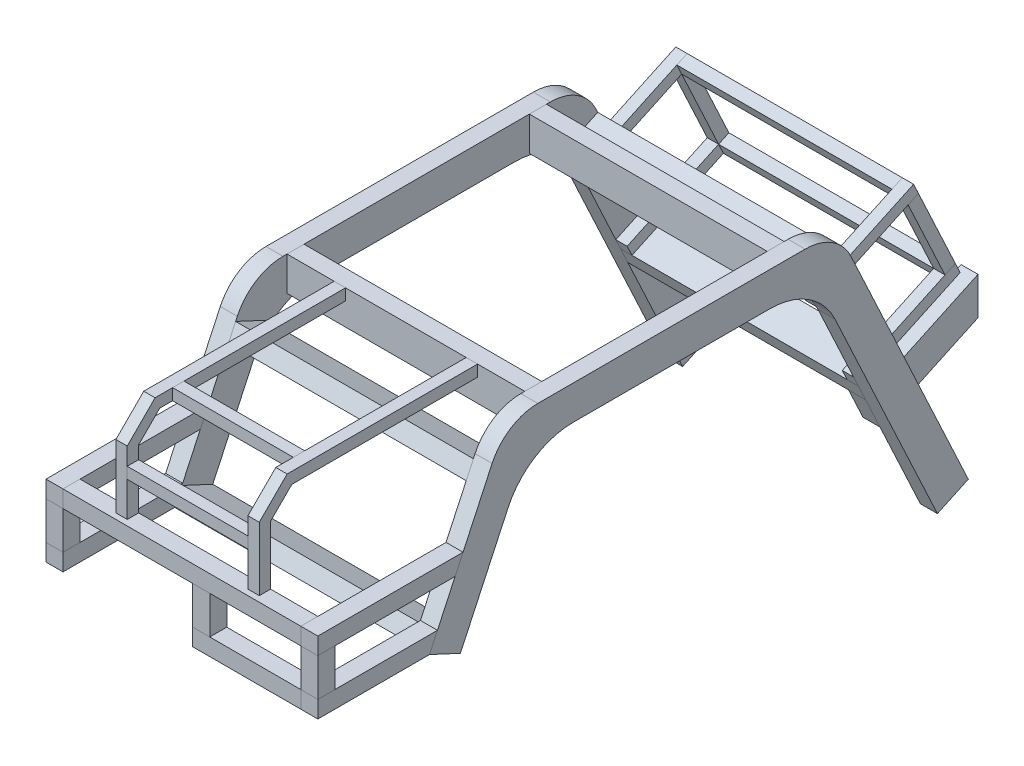
SolidWorks part; units mm, degrees
ref_plane "Front Plane" through (0, 0, 0) normal (0, 0, 1) x (1, 0, 0)
ref_plane "Top Plane" through (0, 0, 0) normal (0, 1, 0) x (1, 0, 0)
ref_plane "Right Plane" through (0, 0, 0) normal (1, 0, 0) x (0, 0, -1)
sketch "Sketch1" plane through (0, 0, 0) normal (1, 0, 0) x (0, 0, -1)
  line L1 (0, 30) -> (0, -30) construction
  line L33 (254, -30) -> (-254, -30)
  line L34 (292.2242, 30) -> (-292.2242, 30)
  line L35 (-372.0795, -283.2224) -> (-254, -30)
  line L36 (-426.458, -257.8653) -> (-292.2242, 30)
  line L39 (468.6901, -490.4044) -> (254, -30)
  line L40 (523.0685, -465.0473) -> (292.2242, 30)
  line L45 (523.0685, -465.0473) -> (468.6901, -490.4044)
  line L46 (-372.0795, -283.2224) -> (-426.458, -257.8653)
  point P2 (0, 0)
  dimension "D1" = 508
  dimension "D2" = 115
  dimension "D3" = 60
  dimension "D4" = 279.4
  dimension "D5" = 508
  dimension "D6" = 60
  dimension "D7" = 60
extrude "Boss-Extrude1" add sketch "Sketch1" against normal blind 30 from offset 239.55
sketch "Sketch2" plane through (239.55, 0, 0) normal (1, 0, 0) x (0, 0, -1)
  line L2 (-426.458, -257.8653) -> (-372.0795, -283.2224) construction
  line L6 (-381.3778, -161.1904) -> (-623.308, -161.1904)
  line L7 (-412.4688, -227.8654) -> (-623.308, -227.8654)
  line L10 (-367.3886, -131.1905) -> (-623.308, -131.1905)
  line L11 (-426.458, -257.8653) -> (-623.308, -257.8653)
  line L12 (-426.458, -257.8653) -> (-292.2242, 30) construction
  line L13 (-367.3886, -131.1905) -> (-381.3778, -161.1904)
  line L14 (-412.4688, -227.8654) -> (-426.458, -257.8653)
  line L15 (-623.308, -131.1905) -> (-623.308, -161.1904)
  line L16 (-623.308, -227.8654) -> (-623.308, -257.8653)
  dimension "D1" = 126.6748
  dimension "D2" = 255.9194
  dimension "D3" = 29.9999
extrude "Boss-Extrude2" add sketch "Sketch2" against normal up to surface (30 mm away) separate body up to face at (209.55, -187.0674, -24.1526)
sketch "Sketch12" plane through (239.55, 0, 0) normal (1, 0, 0) x (0, 0, -1)
  line L0 (-412.4688, -227.8654) -> (-623.308, -227.8654) construction
  line L1 (-623.308, -161.1904) -> (-593.3081, -161.1904)
  line L2 (-623.308, -161.1904) -> (-623.308, -227.8654)
  line L3 (-623.308, -227.8654) -> (-593.3081, -227.8654)
  line L4 (-593.3081, -161.1904) -> (-593.3081, -227.8654)
  line L5 (-623.308, -131.1905) -> (-623.308, -161.1904) construction
extrude "Boss-Extrude11" add sketch "Sketch12" against normal up to surface (30 mm away) separate body up to face at (209.55, -242.8654, 521.3857)
sketch "Sketch3" plane through (209.55, 0, 0) normal (-1, 0, 0) x (0, 0, 1)
  line L2 (228.6, 30) -> (228.6, -30)
  line L3 (264.7345, -53.0202) -> (319.113, -27.6631)
  line L4 (-254, -30) -> (254, -30) construction
  line L5 (292.2242, 30) -> (-292.2242, 30) construction
  line L6 (254, -30) -> (372.0795, -283.2224) construction
  line L7 (264.7345, -53.0202) -> (277.4131, -80.2095)
  line L8 (277.4131, -80.2095) -> (331.7915, -54.8524)
  line L9 (426.458, -257.8653) -> (292.2242, 30) construction
  line L10 (331.7915, -54.8524) -> (319.113, -27.6631)
  line L11 (228.6, 30) -> (198.6, 30)
  line L12 (198.6, 30) -> (198.6, -30)
  line L13 (198.6, -30) -> (228.6, -30)
  line L14 (372.0795, -283.2224) -> (426.458, -257.8653)
  line L15 (623.308, -131.1905) -> (593.3081, -131.1905)
  line L16 (623.308, -131.1905) -> (623.308, -161.1904)
  line L17 (623.308, -161.1904) -> (593.3081, -161.1904)
  line L18 (593.3081, -131.1905) -> (593.3081, -161.1904)
  line L19 (593.3081, -227.8654) -> (623.308, -227.8654)
  line L20 (593.3081, -227.8654) -> (593.3081, -257.8653)
  line L21 (593.3081, -257.8653) -> (623.308, -257.8653)
  line L22 (623.308, -227.8654) -> (623.308, -257.8653)
  line L23 (426.458, -257.8653) -> (413.7795, -230.6761)
  line L24 (413.7795, -230.6761) -> (359.401, -256.0332)
  line L25 (359.401, -256.0332) -> (372.0795, -283.2224)
  line L26 (0, 30) -> (0, -30) construction
  line L27 (-359.401, -256.0332) -> (-372.0795, -283.2224)
  line L28 (-413.7795, -230.6761) -> (-359.401, -256.0332)
  line L29 (-426.458, -257.8653) -> (-413.7795, -230.6761)
  line L30 (-372.0795, -283.2224) -> (-426.458, -257.8653)
  line L31 (-198.6, -30) -> (-228.6, -30)
  line L32 (-198.6, 30) -> (-198.6, -30)
  line L33 (-228.6, 30) -> (-198.6, 30)
  line L34 (-331.7915, -54.8524) -> (-319.113, -27.6631)
  line L35 (-277.4131, -80.2095) -> (-331.7915, -54.8524)
  line L36 (-264.7345, -53.0202) -> (-277.4131, -80.2095)
  line L37 (-264.7345, -53.0202) -> (-319.113, -27.6631)
  line L38 (-228.6, 30) -> (-228.6, -30)
  dimension "D1" = 30
  dimension "D2" = 25.4
  dimension "D3" = 25.4
extrude "Boss-Extrude3" add sketch "Sketch3" along normal blind 419.1 separate body
sketch "Sketch4" plane through (-209.55, 0, 0) normal (-1, 0, 0) x (0, 0, 1)
  line L8 (372.0795, -283.2224) -> (426.458, -257.8653)
  line L9 (254, -30) -> (372.0795, -283.2224)
  line L10 (-254, -30) -> (254, -30)
  line L11 (-468.6901, -490.4044) -> (-254, -30)
  line L12 (-523.0685, -465.0473) -> (-468.6901, -490.4044)
  line L13 (-292.2242, 30) -> (-523.0685, -465.0473)
  line L14 (292.2242, 30) -> (-292.2242, 30)
  line L15 (426.458, -257.8653) -> (292.2242, 30)
  line L16 (372.0795, -283.2224) -> (426.458, -257.8653)
  line L17 (254, -30) -> (372.0795, -283.2224)
  line L18 (-254, -30) -> (254, -30)
  line L19 (-468.6901, -490.4044) -> (-254, -30)
  line L20 (-523.0685, -465.0473) -> (-468.6901, -490.4044)
  line L21 (-292.2242, 30) -> (-523.0685, -465.0473)
  line L22 (292.2242, 30) -> (-292.2242, 30)
  line L23 (426.458, -257.8653) -> (292.2242, 30)
  dimension "D1" = 0
extrude "Boss-Extrude4" add sketch "Sketch4" along normal blind 30 separate body
sketch "Sketch5" plane through (-239.55, 0, 0) normal (-1, 0, 0) x (0, 0, 1)
  line L4 (623.308, -227.8654) -> (412.4688, -227.8654)
  line L6 (623.308, -257.8653) -> (623.308, -227.8654)
  line L7 (426.458, -257.8653) -> (623.308, -257.8653)
  line L8 (412.4688, -227.8654) -> (426.458, -257.8653)
  line L9 (623.308, -227.8654) -> (412.4688, -227.8654)
  line L10 (623.308, -257.8653) -> (623.308, -227.8654)
  line L11 (426.458, -257.8653) -> (623.308, -257.8653)
  line L12 (412.4688, -227.8654) -> (426.458, -257.8653)
  line L13 (381.3778, -161.1904) -> (623.308, -161.1904)
  line L14 (367.3886, -131.1905) -> (381.3778, -161.1904)
  line L15 (623.308, -131.1905) -> (367.3886, -131.1905)
  line L24 (623.308, -161.1904) -> (623.308, -131.1905)
  line L25 (381.3778, -161.1904) -> (623.308, -161.1904)
  line L26 (367.3886, -131.1905) -> (381.3778, -161.1904)
  line L27 (623.308, -131.1905) -> (367.3886, -131.1905)
  line L28 (623.308, -161.1904) -> (623.308, -131.1905)
  dimension "D1" = 0
  dimension "D2" = 0
extrude "Boss-Extrude5" add sketch "Sketch5" against normal up to surface (30 mm away) separate body up to face at (-209.55, -146.1905, 608.3081)
sketch "Sketch13" plane through (-239.55, 0, 0) normal (-1, 0, 0) x (0, 0, 1)
  line L4 (623.308, -161.1904) -> (593.3081, -161.1904)
  line L5 (593.3081, -161.1904) -> (593.3081, -227.8654)
  line L6 (593.3081, -227.8654) -> (623.308, -227.8654)
  line L7 (623.308, -227.8654) -> (623.308, -161.1904)
  line L8 (623.308, -161.1904) -> (593.3081, -161.1904)
  line L9 (593.3081, -161.1904) -> (593.3081, -227.8654)
  line L10 (593.3081, -227.8654) -> (623.308, -227.8654)
  line L11 (623.308, -227.8654) -> (623.308, -161.1904)
  dimension "D1" = 0
extrude "Boss-Extrude12" add sketch "Sketch13" against normal up to surface (30 mm away) separate body up to face at (-209.55, -146.1905, 498.8456)
sketch "Sketch6" plane through (-209.55, 0, 0) normal (-1, 0, 0) x (0, 0, 1)
  line L6 (-456.6807, 3.3844) -> (-277.4131, -80.2095)
  line L7 (-285.8654, -98.3356) -> (-465.1331, -14.7417)
  line L10 (-530.2163, -154.3131) -> (-350.9486, -237.907)
  line L11 (-538.6687, -172.4393) -> (-359.401, -256.0332)
  line L12 (-277.4131, -80.2095) -> (-285.8654, -98.3356)
  line L13 (-350.9486, -237.907) -> (-359.401, -256.0332)
  line L14 (-468.6901, -490.4044) -> (-254, -30) construction
  line L15 (-456.6807, 3.3844) -> (-465.1331, -14.7417)
  line L16 (-530.2163, -154.3131) -> (-538.6687, -172.4393)
  dimension "D1" = 20
  dimension "D2" = 197.8
extrude "Boss-Extrude6" add sketch "Sketch6" against normal blind 20 separate body
sketch "Sketch14" plane through (-209.55, 0, 0) normal (-1, 0, 0) x (0, 0, 1)
  line L0 (-465.1331, -14.7417) -> (-530.2163, -154.3131)
  line L1 (-530.2163, -154.3131) -> (-512.0902, -162.7655)
  line L2 (-350.9486, -237.907) -> (-530.2163, -154.3131) construction
  line L3 (-512.0902, -162.7655) -> (-447.0069, -23.1941)
  line L4 (-465.1331, -14.7417) -> (-285.8654, -98.3356) construction
  line L5 (-447.0069, -23.1941) -> (-465.1331, -14.7417)
  line L6 (-456.6807, 3.3844) -> (-465.1331, -14.7417) construction
extrude "Boss-Extrude13" add sketch "Sketch14" against normal up to surface (20 mm away) separate body up to face at (-189.55, -47.4756, -371.2731)
ref_plane "Mid" through (0, 0, 0) normal (-1, 0, 0) x (0, 0, 1)
ref_plane "Half" through (0, 0, 0) normal (0, 0, -1) x (-1, 0, 0)
mirror "Mirror1" about plane through (0, 0, 0) normal (-1, 0, 0) of bodies 131 130 132 114
sketch "Sketch7" plane through (189.55, 0, 0) normal (-1, 0, 0) x (0, 0, 1)
  line L0 (-447.0069, -23.1941) -> (-438.5546, -5.0679)
  line L1 (-277.4131, -80.2095) -> (-456.6807, 3.3844) construction
  line L2 (-438.5546, -5.0679) -> (-456.6807, 3.3844)
  line L3 (-456.6807, 3.3844) -> (-465.1331, -14.7417)
  line L4 (-512.0902, -162.7655) -> (-447.0069, -23.1941) construction
  line L5 (-465.1331, -14.7417) -> (-447.0069, -23.1941)
  line L6 (-512.0902, -162.7655) -> (-520.5425, -180.8916)
  line L7 (-538.6687, -172.4393) -> (-359.401, -256.0332) construction
  line L8 (-520.5425, -180.8916) -> (-538.6687, -172.4393)
  line L9 (-538.6687, -172.4393) -> (-530.2163, -154.3131)
  line L10 (-530.2163, -154.3131) -> (-512.0902, -162.7655)
  line L11 (-350.9486, -237.907) -> (-530.2163, -154.3131) construction
extrude "Boss-Extrude7" add sketch "Sketch7" along normal up to surface (379.1 mm away) separate body up to face at (-189.55, -205.1731, -444.8087)
ref_plane "Sensor Mount" through (-126.36, 0, 0) normal (1, 0, 0) x (0, 0, -1)
sketch "Sketch8" plane through (-126.36, 0, 0) normal (-1, 0, 0) x (0, 0, 1)
  line L2 (613.3081, -19.0833) -> (613.3081, -131.1905)
  line L3 (593.3081, -27.3676) -> (593.3081, -131.1905)
  line L6 (613.3081, -19.0833) -> (564.2248, 30)
  line L7 (555.9405, 10) -> (593.3081, -27.3676)
  line L10 (564.2248, 30) -> (228.6, 30)
  line L11 (555.9405, 10) -> (228.6, 10)
  line L12 (228.6, 30) -> (228.6, 10)
  line L13 (593.3081, -131.1905) -> (613.3081, -131.1905)
  dimension "D1" = 45
  dimension "D2" = 20
  dimension "D3" = 20
  dimension "D4" = 20
  dimension "D5" = 103.823
extrude "Boss-Extrude8" add sketch "Sketch8" against normal blind 20 separate body
mirror "Mirror2" about plane through (0, 0, 0) normal (-1, 0, 0) of bodies 118
sketch "Sketch9" plane through (-106.36, 0, 0) normal (1, 0, 0) x (0, 0, -1)
  line L2 (-533.3106, 30) -> (-533.3106, 10)
  line L3 (-613.3081, -49.9975) -> (-593.3081, -49.9975)
  line L4 (-613.3081, -131.1905) -> (-613.3081, -19.0833) construction
  line L6 (-228.6, 10) -> (-555.9405, 10) construction
  line L8 (-533.3106, 30) -> (-513.3106, 30)
  line L9 (-564.2248, 30) -> (-228.6, 30) construction
  line L10 (-513.3106, 30) -> (-513.3106, 10)
  line L11 (-513.3106, 10) -> (-533.3106, 10)
  line L12 (-593.3081, -49.9975) -> (-593.3081, -69.9975)
  line L13 (-593.3081, -27.3676) -> (-593.3081, -131.1905) construction
  line L14 (-593.3081, -69.9975) -> (-613.3081, -69.9975)
  line L15 (-613.3081, -69.9975) -> (-613.3081, -49.9975)
  dimension "D1" = 20
  dimension "D2" = 22.6299
  dimension "D3" = 22.6299
extrude "Boss-Extrude9" add sketch "Sketch9" along normal up to surface (212.72 mm away) separate body up to face at (106.36, -28.604, 498.8247)
sketch "Sketch10" plane through (0, 0, 623.308) normal (0, 0, 1) x (1, 0, 0)
  line L5 (209.55, -237.907) -> (209.55, -154.3131) construction
  line L7 (19.0501, -227.8654) -> (19.0501, -161.1904)
  line L8 (19.0501, -161.1904) -> (49.0501, -161.1904)
  line L10 (49.0501, -161.1904) -> (49.0501, -227.8654)
  line L12 (49.0501, -227.8654) -> (19.0501, -227.8654)
  line L13 (-209.55, -227.8654) -> (209.55, -227.8654) construction
  line L14 (-209.55, -161.1904) -> (209.55, -161.1904) construction
  dimension "D1" = 30
  dimension "D2" = 190.4999
extrude "Boss-Extrude10" add sketch "Sketch10" against normal blind 30 separate body
sketch "Sketch11" plane through (0, 0, 623.308) normal (0, 0, 1) x (1, 0, 0)
  line L0 (-209.55, -257.8653) -> (209.55, -257.8653) construction
  line L1 (-209.55, -227.8654) -> (19.0501, -227.8654)
  line L2 (-209.55, -227.8654) -> (-209.55, -257.8653)
  line L3 (-209.55, -257.8653) -> (19.0501, -257.8653)
  line L4 (19.0501, -227.8654) -> (19.0501, -257.8653)
extrude "Cut-Extrude1" cut sketch "Sketch11" against normal up to next (29.9999 mm away)
sketch "Sketch15" plane through (209.55, 0, 0) normal (-1, 0, 0) x (0, 0, 1)
  line L2 (-397.4366, -337.6009) -> (-570.185, -257.047)
  line L3 (-372.0795, -283.2224) -> (-570.185, -190.8443)
  line L5 (-254, -30) -> (-468.6901, -490.4044) construction
  line L7 (-372.0795, -283.2224) -> (-397.4366, -337.6009)
  line L8 (-570.185, -257.047) -> (-570.185, -190.8443)
  dimension "D1" = 60
  dimension "D2" = 218.5852
extrude "Boss-Extrude14" add sketch "Sketch15" along normal blind 30 separate body
sketch "Wheels" plane through (0, 0, 0) normal (1, 0, 0) x (0, 0, -1)
  line L0 (0, 30) -> (0, -30) construction
  line L1 (292.2242, 30) -> (-292.2242, 30) construction
  line L2 (-254, -30) -> (254, -30) construction
  circle A1 centre (522.935, -404.42) radius 165.1
  circle A2 centre (-522.935, -404.42) radius 165.1
  dimension "D1" = 1045.87
  dimension "D2" = 330.2
  dimension "D3" = 404.42
sketch "Sketch17" plane through (136.426, 0, 0) normal (1, 0, 0) x (0, 0, -1)
  line L1 (468.6901, -490.4044) -> (523.0685, -465.0473) construction
  line L2 (523.0685, -465.0473) -> (426.458, -257.8653) construction
  line L3 (523.0685, -465.0473) -> (292.2242, 30) construction
  line L4 (426.458, -257.8653) -> (372.0795, -283.2224) construction
  line L5 (254, -30) -> (468.6901, -490.4044) construction
  line L6 (372.0795, -283.2224) -> (468.6901, -490.4044) construction
  line L7 (-372.0795, -283.2224) -> (372.0795, -283.2224) construction
  line L8 (399.2688, -270.5438) -> (495.8793, -477.7258) construction
  line L9 (420.3848, -386.8134) -> (474.7633, -361.4563) construction
  line L10 (447.574, -374.1348) -> (488.2744, -374.1348) construction
  circle A0 centre (560.9187, -386.7116) radius 52.5
  circle A2 centre (-522.935, -404.42) radius 165.1 construction
  circle A3 centre (-522.935, -404.42) radius 165.1 construction
  dimension "D1" = 105
  dimension "D11" = 330.2
  dimension "D2" = 560.9187
  dimension "D3" = 386.7116
  dimension "D4" = 522.935
  dimension "D5" = 404.42
  dimension "D6" = 60
  dimension "D7" = 228.6
  dimension "D8" = 115
  dimension "D9" = 447.574
  dimension "D10" = 374.1348
extrude "Boss-Extrude15" [suppressed] add sketch "Sketch17" along normal blind 144.65
mirror "Mirror3" [suppressed] about plane through (0, 0, 0) normal (-1, 0, 0)
mirror "Mirror4" [suppressed] about plane through (0, 0, 0) normal (0, 0, -1)
sketch "Collision" [suppressed] plane through (0, 0, -228.6) normal (0, 0, -1) x (-1, 0, 0)
  line L0 (-208.751, -334.2116) -> (-208.751, -439.2116) construction
  line L1 (-136.426, -334.2116) -> (-281.076, -334.2116) construction
  line L2 (-281.076, -439.2116) -> (-136.426, -439.2116) construction
  line L3 (-281.076, -386.7116) -> (-136.426, -386.7116) construction
  line L4 (-281.076, -334.2116) -> (-281.076, -439.2116) construction
  line L5 (-136.426, -439.2116) -> (-136.426, -334.2116) construction
  line L6 (-224.55, -490.4044) -> (-224.55, -465.0473) construction
  line L7 (-209.55, -490.4044) -> (-239.55, -490.4044) construction
  line L8 (-209.55, -465.0473) -> (-239.55, -465.0473) construction
  dimension "D1" = 208.751
  dimension "D2" = 144.65
  dimension "D3" = 224.55
fillet "Fillet1" radius 88.9 2 edges at (224.55, 30, -292.2242) (224.55, 30, 292.2242)
fillet "Fillet2" radius 88.9 2 edges at (-224.55, 30, -292.2242) (-224.55, 30, 292.2242)
fillet "Fillet3" radius 127 2 edges at (224.55, -30, -254) (224.55, -30, 254)
fillet "Fillet4" radius 127 2 edges at (-224.55, -30, -254) (-224.55, -30, 254)
